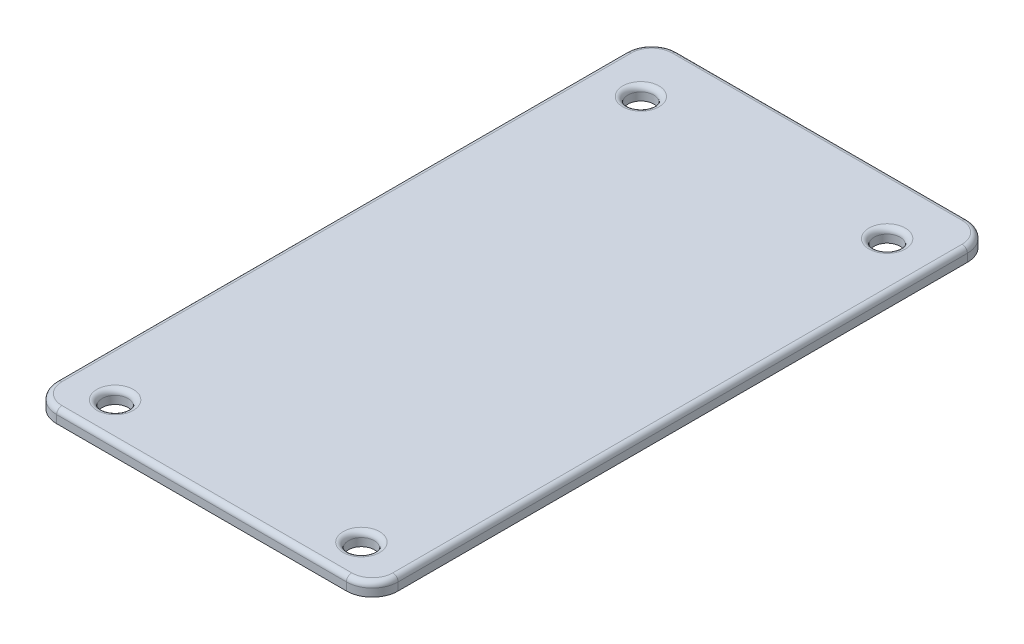
SolidWorks part; units mm, degrees
ref_plane "Front Plane" through (0, 0, 0) normal (0, 0, 1) x (1, 0, 0)
ref_plane "Top Plane" through (0, 0, 0) normal (0, 1, 0) x (1, 0, 0)
ref_plane "Right Plane" through (0, 0, 0) normal (1, 0, 0) x (0, 0, -1)
sketch "Sketch1" plane through (0, 0, 0) normal (0, 1, 0) x (1, 0, 0)
  line L1 (0.4896, 8.6117) -> (33.4896, 8.6117)
  line L2 (0.4896, 8.6117) -> (0.4896, -51.3883)
  line L3 (0.4896, -51.3883) -> (33.4896, -51.3883)
  line L4 (33.4896, 8.6117) -> (33.4896, -51.3883)
extrude "Boss-Extrude1" add sketch "Sketch1" along normal blind 1.27
sketch "Sketch2" plane through (0, 1.27, 0) normal (0, 1, 0) x (1, 0, 0)
  line L0 (3.8396, 2.9617) -> (50003.8396, 2.9617) construction
  line L1 (5.0896, 4.2117) -> (5.0896, -49995.7883) construction
  line L2 (28.8896, 4.2117) -> (28.8896, -49995.7883) construction
  line L3 (30.1396, -47.8383) -> (-49969.8604, -47.8383) construction
  circle A4 centre (5.0939, 2.9617) radius 1.2457
  circle A5 centre (28.8896, 2.9617) radius 1.25
  circle A6 centre (5.0896, -47.8383) radius 1.25
  circle A7 centre (28.8896, -47.8383) radius 1.25
extrude "Cut-Extrude1" cut sketch "Sketch2" against normal up to next
fillet "Fillet1" radius 2.5 4 edges at (33.4896, 0.635, 51.3883) (0.4896, 0.635, 51.3883) (0.4896, 0.635, -8.6117) (33.4896, 0.635, -8.6117)
fillet "Fillet2" radius 0.508 12 edges at (1.2218, 1.27, 50.6561) (0.4896, 1.27, 21.3883) (1.2218, 1.27, -7.8795) (16.9896, 1.27, -8.6117) (32.7574, 1.27, -7.8795) (33.4896, 1.27, 21.3883) (32.7574, 1.27, 50.6561) (16.9896, 1.27, 51.3883) (5.0939, 1.27, -1.716) (28.8896, 1.27, 49.0883) (5.0896, 1.27, 49.0883) (28.8896, 1.27, -1.7117)
